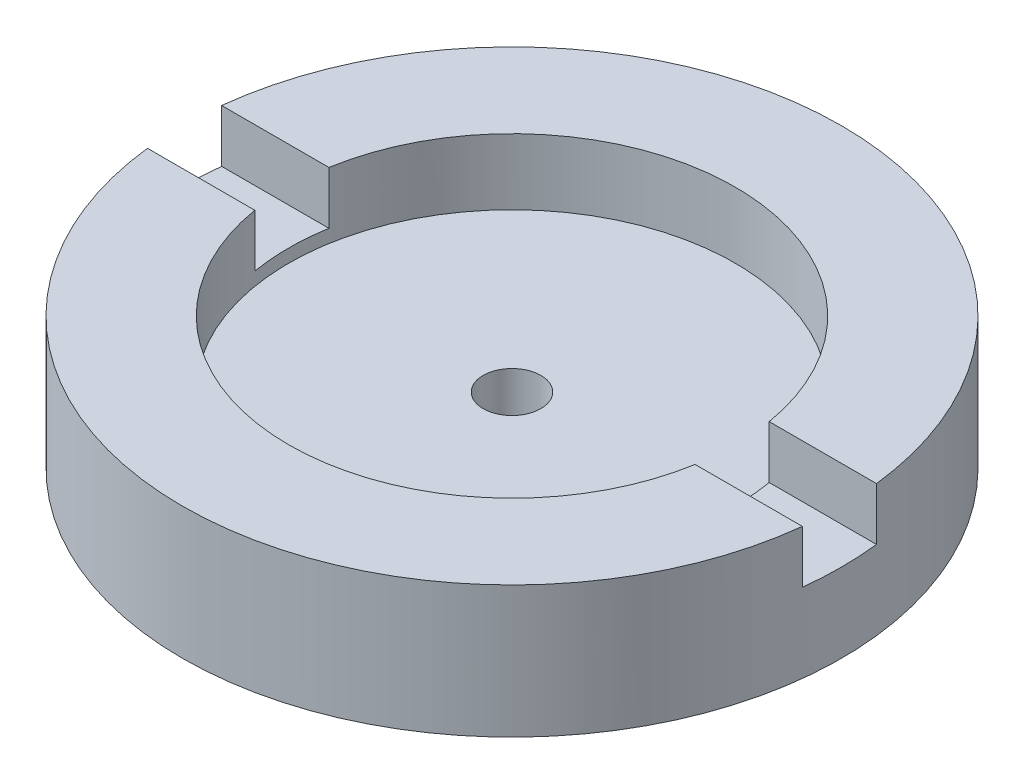
SolidWorks part; units mm, degrees
ref_plane "Piano frontale" through (0, 0, 0) normal (0, 0, 1) x (1, 0, 0)
ref_plane "Piano superiore" through (0, 0, 0) normal (0, 1, 0) x (1, 0, 0)
ref_plane "Piano destro" through (0, 0, 0) normal (1, 0, 0) x (0, 0, -1)
sketch "Schizzo1" plane through (0, 0, 0) normal (0, 1, 0) x (1, 0, 0)
  circle A0 centre (0, 0) radius 20
extrude "Estrusione-Estrusione1" add sketch "Schizzo1" along normal blind 8
sketch "Schizzo2" plane through (0, 8, 0) normal (0, 1, 0) x (1, 0, 0)
  circle A0 centre (0, 0) radius 13.55
  dimension "D1" = 27.1
extrude "Taglio-Estrusione1" cut sketch "Schizzo2" against normal blind 4
sketch "Schizzo3" plane through (0, 8, 0) normal (0, 1, 0) x (1, 0, 0)
  line L1 (28.0656, -2.25) -> (-28.0656, -2.25)
  line L2 (28.0656, -2.25) -> (28.0656, 2.25)
  line L3 (28.0656, 2.25) -> (-28.0656, 2.25)
  line L4 (-28.0656, -2.25) -> (-28.0656, 2.25)
  line L5 (28.0656, -2.25) -> (-28.0656, 2.25) construction
  line L6 (28.0656, 2.25) -> (-28.0656, -2.25) construction
  point P0 (0, 0)
  dimension "D1" = 4.5
extrude "Taglio-Estrusione2" cut sketch "Schizzo3" against normal blind 3.2
sketch "Schizzo4" plane through (0, 0, 0) normal (0, -1, 0) x (1, 0, 0)
  circle A0 centre (0, 0) radius 1.75
extrude "Taglio-Estrusione3" cut sketch "Schizzo4" against normal through all
